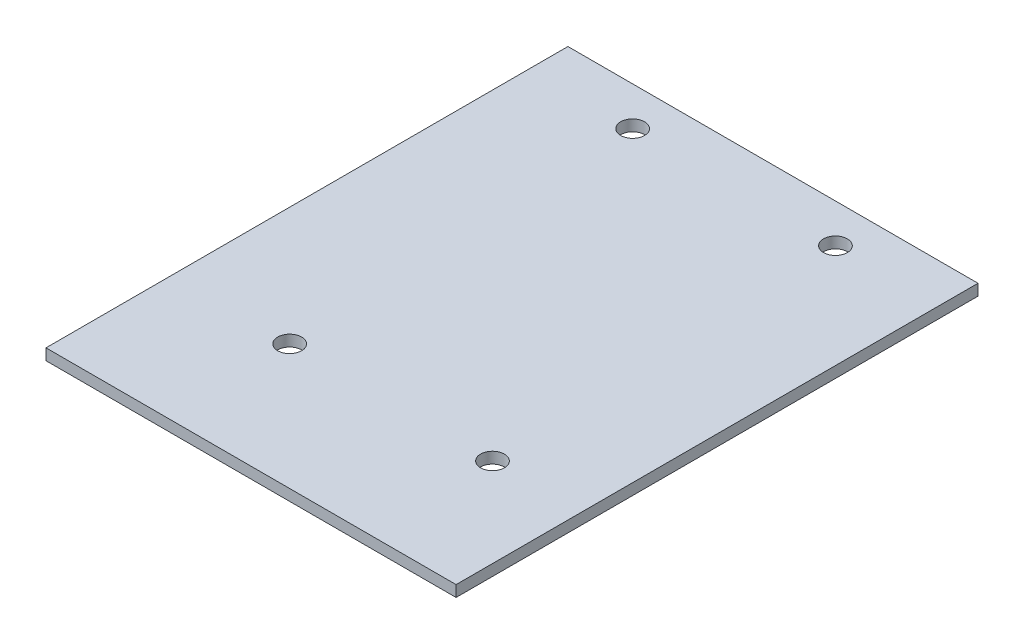
SolidWorks part; units mm, degrees
ref_plane "Ebene vorne" through (0, 0, 0) normal (0, 0, 1) x (1, 0, 0)
ref_plane "Ebene oben" through (0, 0, 0) normal (0, 1, 0) x (1, 0, 0)
ref_plane "Ebene rechts" through (0, 0, 0) normal (1, 0, 0) x (0, 0, -1)
sketch "Skizze1" plane through (0, 0, 0) normal (0, 1, 0) x (1, 0, 0)
  line L1 (0, 0) -> (55, 0)
  line L2 (0, 0) -> (0, 70)
  line L3 (0, 70) -> (55, 70)
  line L4 (55, 0) -> (55, 70)
  dimension "D1" = 70
  dimension "D2" = 55
extrude "Aufsatz-Linear austragen1" add sketch "Skizze1" along normal blind 1.5
sketch "Skizze2" plane through (0, 1.5, 0) normal (0, 1, 0) x (1, 0, 0)
  line L1 (0, 0) -> (55, 0) construction
  circle A0 centre (13.8808, 64.8) radius 1.6
  circle A1 centre (41.0808, 64.8) radius 1.6
  circle A2 centre (15.8808, 16.8) radius 1.6
  circle A3 centre (43.0808, 16.8) radius 1.6
  dimension "D1" = 3.2
  dimension "D2" = 3.2
  dimension "D3" = 3.2
  dimension "D4" = 3.2
  dimension "D5" = 27.2
  dimension "D6" = 27.2
  dimension "D7" = 48
  dimension "D8" = 48
  dimension "D9" = 2
  dimension "D10" = 64.8
extrude "Schnitt-Linear austragen1" cut sketch "Skizze2" against normal up to surface (1.5 mm away) up to face at (27.5, 0, -35)
